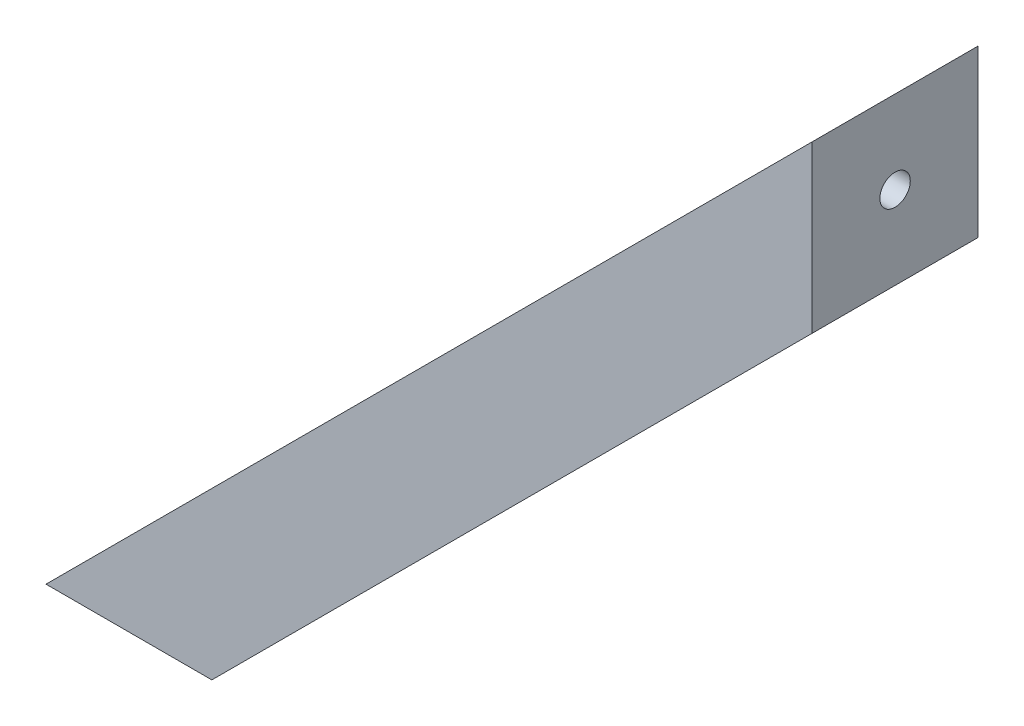
SolidWorks part; units mm, degrees
ref_plane "Front Plane" through (0, 0, 0) normal (0, 0, 1) x (1, 0, 0)
ref_plane "Top Plane" through (0, 0, 0) normal (0, 1, 0) x (1, 0, 0)
ref_plane "Right Plane" through (0, 0, 0) normal (1, 0, 0) x (0, 0, -1)
sketch "Sketch1" plane through (0, 0, 0) normal (0, 0, 1) x (1, 0, 0)
  line L0 (0, 0) -> (176.013, 176.013)
  line L1 (176.013, 176.013) -> (176.013, 137.913)
  line L2 (176.013, 137.913) -> (38.1, 0)
  line L3 (38.1, 0) -> (0, 0)
  dimension "D1" = 38.1
  dimension "D2" = 38.1
  dimension "D3" = 45
  dimension "D4" = 45
  dimension "D5" = 248.92
extrude "Boss-Extrude1" add sketch "Sketch1" along normal blind 38.1
ref_plane "Plane1" through (-1.7961, 1.7961, 0) normal (-0.7071, 0.7071, 0) x (0, 0, 1)
shell "Shell1" thickness 6.35
sketch "Sketch3" plane through (0, 0, 0) normal (0, -1, 0) x (1, 0, 0)
  line L0 (19.05, 38.1) -> (19.05, 0) construction
  line L1 (0, 38.1) -> (38.1, 38.1) construction
  line L2 (0, 0) -> (38.1, 0) construction
  line L3 (19.05, 0) -> (0, 19.05) construction
  line L4 (0, 38.1) -> (0, 0) construction
  line L5 (0, 19.05) -> (38.1, 19.05) construction
  line L6 (38.1, 38.1) -> (38.1, 0) construction
  circle A0 centre (19.05, 19.05) radius 3.4925
  dimension "D1" = 6.985
extrude "Cut-Extrude1" cut sketch "Sketch3" against normal up to surface (6.35 mm away) up to face at (20.9099, 6.35, 19.05)
sketch "Sketch4" plane through (176.013, 0, 0) normal (1, 0, 0) x (0, 0, -1)
  line L0 (-19.05, 176.013) -> (-19.05, 137.913) construction
  line L1 (-38.1, 176.013) -> (0, 176.013) construction
  line L2 (-38.1, 137.913) -> (0, 137.913) construction
  line L3 (-19.05, 137.913) -> (-38.1, 156.963) construction
  line L4 (-38.1, 137.913) -> (-38.1, 176.013) construction
  line L5 (-38.1, 156.963) -> (0, 156.963) construction
  line L6 (0, 137.913) -> (0, 176.013) construction
  circle A0 centre (-19.05, 156.963) radius 3.4925
  dimension "D1" = 6.985
extrude "Cut-Extrude2" cut sketch "Sketch4" against normal blind 59.436
sketch "Sketch6" plane through (0, 0, 0) normal (-0.7071, 0.7071, 0) x (0, 0, 1)
  line L0 (6.35, 239.9397) -> (6.35, 8.9803) construction
  line L1 (6.35, 121.158) -> (31.75, 121.158)
  line L2 (6.35, 121.158) -> (6.35, 127.508)
  line L3 (6.35, 127.508) -> (31.75, 127.508)
  line L4 (31.75, 121.158) -> (31.75, 127.508)
  line L5 (31.75, 239.9397) -> (31.75, 8.9803) construction
  line L6 (38.1, 0) -> (0, 0) construction
  line L7 (6.35, 178.308) -> (31.75, 178.308)
  line L8 (6.35, 178.308) -> (6.35, 171.958)
  line L9 (6.35, 171.958) -> (31.75, 171.958)
  line L10 (31.75, 178.308) -> (31.75, 171.958)
  line L11 (6.35, 76.708) -> (31.75, 76.708)
  line L12 (6.35, 76.708) -> (6.35, 70.358)
  line L13 (6.35, 70.358) -> (31.75, 70.358)
  line L14 (31.75, 76.708) -> (31.75, 70.358)
  dimension "D1" = 6.35
  dimension "D2" = 6.35
  dimension "D3" = 6.35
  dimension "D4" = 121.158
  dimension "D5" = 44.45
  dimension "D6" = 44.45
extrude "Boss-Extrude2" add sketch "Sketch6" against normal up to surface (26.9408 mm away)
